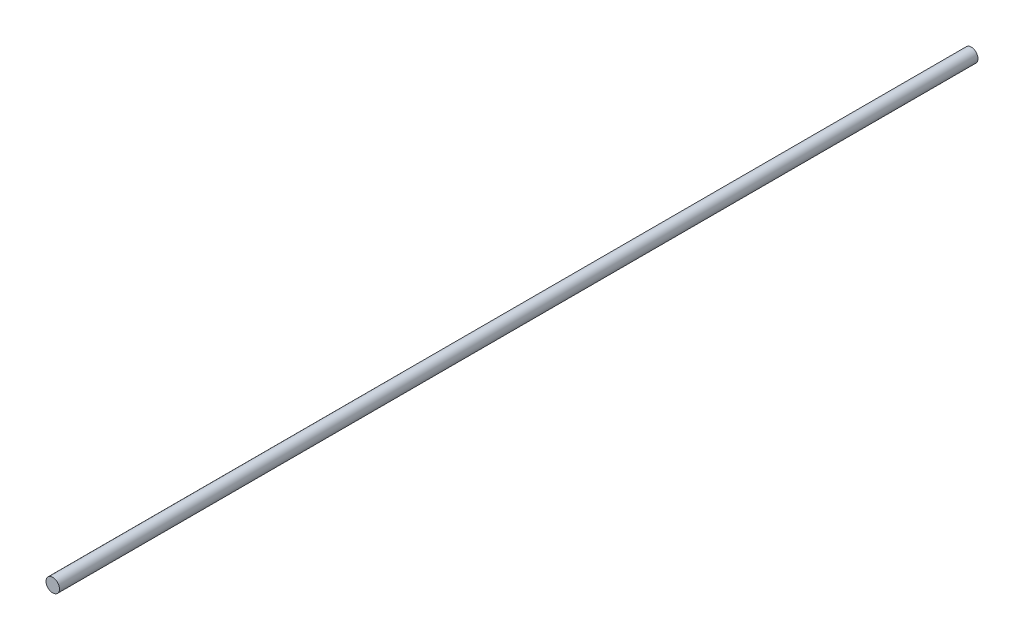
SolidWorks part; units mm, degrees
ref_plane "Front" through (0, 0, 0) normal (0, 0, 1) x (1, 0, 0)
ref_plane "Top" through (0, 0, 0) normal (0, 1, 0) x (1, 0, 0)
ref_plane "Right" through (0, 0, 0) normal (1, 0, 0) x (0, 0, -1)
sketch "스케치1" plane through (0, 0, 0) normal (0, 0, 1) x (1, 0, 0)
  circle A0 centre (0, 0) radius 1.5875
  dimension "D1" = 3.175
extrude "보스-돌출1" add sketch "스케치1" along normal blind 215.9
